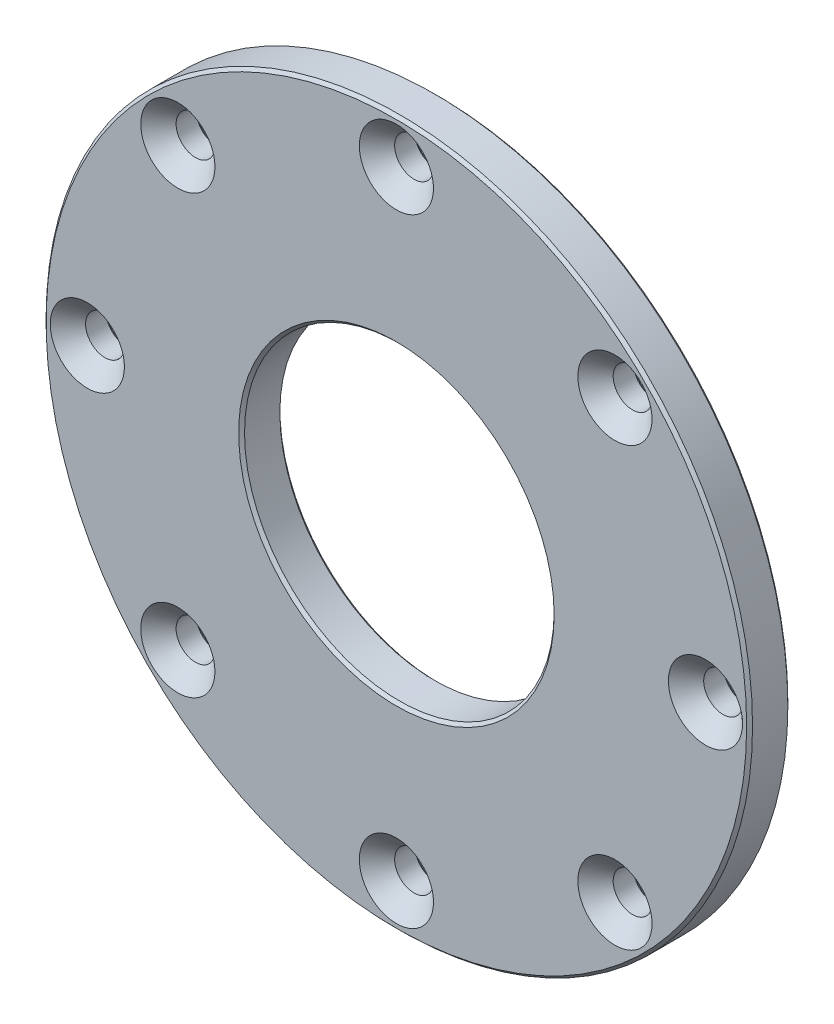
SolidWorks part; units mm, degrees
material "Polylactic Acid (PLA)"
ref_plane "Front Plane" through (0, 0, 0) normal (0, 0, 1) x (1, 0, 0)
ref_plane "Top Plane" through (0, 0, 0) normal (0, 1, 0) x (1, 0, 0)
ref_plane "Right Plane" through (0, 0, 0) normal (1, 0, 0) x (0, 0, -1)
sketch "Sketch1" plane through (0, 0, 0) normal (0, 0, 1) x (1, 0, 0)
  circle A0 centre (0, 0) radius 60
  circle A1 centre (0, 0) radius 26.3
  dimension "D1" = 120
  dimension "D2" = 52.6
extrude "Boss-Extrude1" add sketch "Sketch1" along normal blind 7
sketch "Sketch2" plane through (0, 0, 7) normal (0, 0, 1) x (1, 0, 0)
  circle A0 centre (0, 0) radius 52.5
  circle A1 centre (0, 0) radius 60 construction
  point P5 (0, 52.5)
  point P8 (37.1231, 37.1231)
  point P9 (52.5, 0)
  point P10 (37.1231, -37.1231)
  point P11 (0, -52.5)
  point P12 (-37.1231, -37.1231)
  point P13 (-52.5, 0)
  point P14 (-37.1231, 37.1231)
  dimension "D1" = 7.5
  dimension "D2" = 8
hole_wizard "CSK for M6 Countersunk Flat Head Screw1" positions "Sketch2" profile "Sketch3" countersink size "M6" standard "ISO" end condition through all
sketch "Sketch3" plane through (-37.1231, 37.1231, 7) normal (1, 0, 0) x (0, -1, 0)
  line L0 (0, 0) -> (0, 7)
  line L1 (0, 7) -> (3.3, 7)
  line L2 (3.3, 7) -> (3.3, 3)
  line L3 (3.3, 3) -> (6.3, 0)
  line L5 (6.3, 0) -> (0, 0)
  line L6 (-3.3, 3) -> (-6.3, 0) construction
  line L11 (0, -6.35) -> (0, 107.95) construction
  dimension "Thru Hole Dia." = 6.6
  dimension "Thru Hole Depth" = 7
  dimension "Near C'Sink Dia." = 12.6
  dimension "Near C'Sink Angle" = 90
chamfer "Chamfer1" distance 0.5 angle 45 12 edges at (-33.8231, 37.1231, 0) (-49.2, 0, 0) (-33.8231, -37.1231, 0) (3.3, -52.5, 0) (40.4231, -37.1231, 0) (55.8, 0, 0) (40.4231, 37.1231, 0) (3.3, 52.5, 0) (60, 0, 0) (60, 0, 7) (26.3, 0, 0) (26.3, 0, 7)
